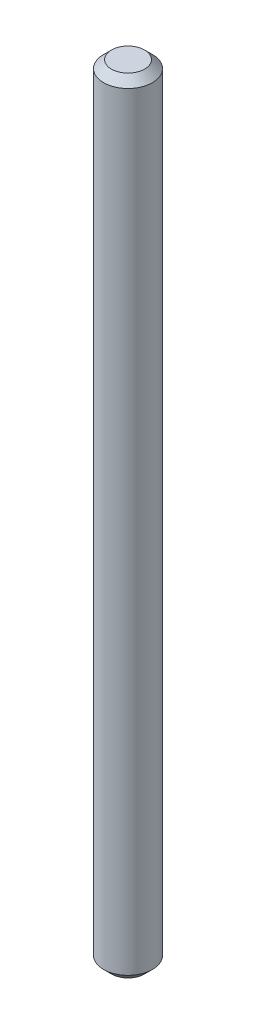
SolidWorks part; units mm, degrees
material "AISI 303 Stainless"
ref_plane "Front Plane" through (0, 0, 0) normal (0, 0, 1) x (1, 0, 0)
ref_plane "Top Plane" through (0, 0, 0) normal (0, 1, 0) x (1, 0, 0)
ref_plane "Right Plane" through (0, 0, 0) normal (1, 0, 0) x (0, 0, -1)
other "Configuration Table"
sketch "Sketch1" plane through (0, 0, 0) normal (0, 0, 1) x (1, 0, 0)
  line L0 (1.0757, 50.8) -> (0, 50.8)
  line L1 (0, 50.8) -> (0, 0)
  line L2 (0, 0) -> (1.0757, 0)
  line L3 (1.0757, 0) -> (1.5837, 0.508)
  line L4 (1.5837, 0.508) -> (1.5837, 50.292)
  line L5 (1.5837, 50.292) -> (1.0757, 50.8)
  line L6 (0, 50.8) -> (0, 0) construction
  dimension "D1" = 1.0757
  dimension "D2" = 1.5837
  dimension "D3" = 50.292
revolve "Revolve1" add sketch "Sketch1" angle 360 about L6
